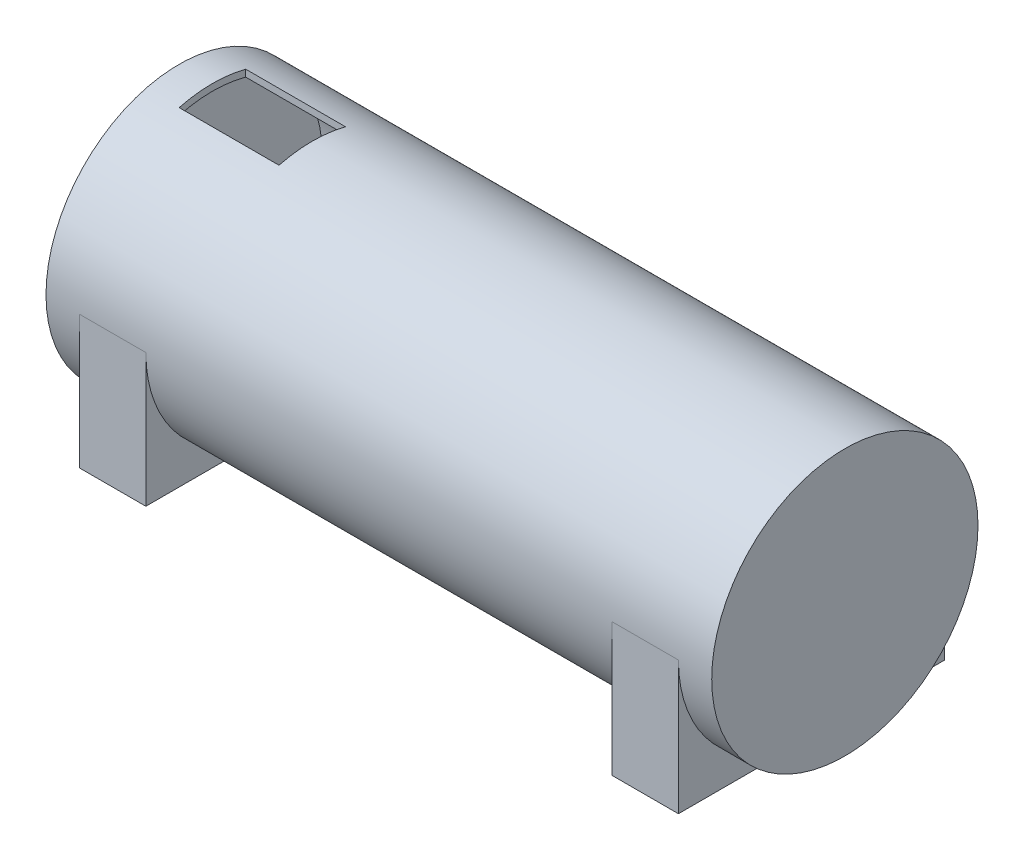
SolidWorks part; units mm, degrees
ref_plane "Ön Düzlem" through (0, 0, 0) normal (0, 0, 1) x (1, 0, 0)
ref_plane "Üst Düzlem" through (0, 0, 0) normal (0, 1, 0) x (1, 0, 0)
ref_plane "Sağ Düzlem" through (0, 0, 0) normal (1, 0, 0) x (0, 0, -1)
sketch "Çizim1" plane through (0, 0, 0) normal (0, 0, 1) x (1, 0, 0)
  line L0 (100, 0) -> (-100, 0) construction
  line L1 (-100, 0) -> (-100, 40)
  line L2 (-100, 40) -> (100, 40)
  line L3 (100, 40) -> (100, 0)
  line L4 (-100, 0) -> (100, 0)
  point P4 (0, 0)
  dimension "D1" = 200
  dimension "D2" = 40
revolve "Döndür1" add sketch "Çizim1" angle 360 about L0
ref_plane "Düzlem1" through (-95, 0, 0) normal (1, 0, 0) x (0, 0, -1)
sketch "Çizim2" plane through (-95, 0, 0) normal (1, 0, 0) x (0, 0, -1)
  circle A0 centre (0, 0) radius 38
  dimension "D1" = 76
extrude "Kes-Ekstrüzyon2" cut sketch "Çizim2" along normal blind 190
ref_plane "Düzlem2" through (0, 40, 0) normal (0, 1, 0) x (1, 0, 0)
sketch "Çizim3" plane through (0, 40, 0) normal (0, 1, 0) x (1, 0, 0)
  line L5 (-90, 10) -> (-60, 10)
  line L6 (-90, 10) -> (-90, -10)
  line L7 (-90, -10) -> (-60, -10)
  line L8 (-60, 10) -> (-60, -10)
  line L9 (-90, 10) -> (-60, -10) construction
  line L10 (-90, -10) -> (-60, 10) construction
  point P0 (-75, 0)
  dimension "D1" = 75
  dimension "D2" = 20
  dimension "D3" = 30
extrude "Kes-Ekstrüzyon3" cut sketch "Çizim3" against normal blind 10
ref_plane "Düzlem3" through (80, 0, 0) normal (1, 0, 0) x (0, 0, -1)
sketch "Çizim5" plane through (80, 0, 0) normal (1, 0, 0) x (0, 0, -1)
  line L0 (0, 0) -> (0, -40) construction
  line L1 (-40, 0) -> (-40, -40)
  line L2 (-40, -40) -> (0, -40)
  circle A0 centre (0, 0) radius 40 construction
  circle A1 centre (0, 0) radius 40
extrude "Yükseklik-Ekstrüzyon1" add sketch "Çizim5" along normal mid plane 20 contours A1 L1 L2
mirror "Aynalama1" about plane through (0, 0, 0) normal (0, 0, 1) of "Yükseklik-Ekstrüzyon1"
mirror "Aynalama2" about plane through (0, 0, 0) normal (1, 0, 0) of "Aynalama1", "Yükseklik-Ekstrüzyon1"
